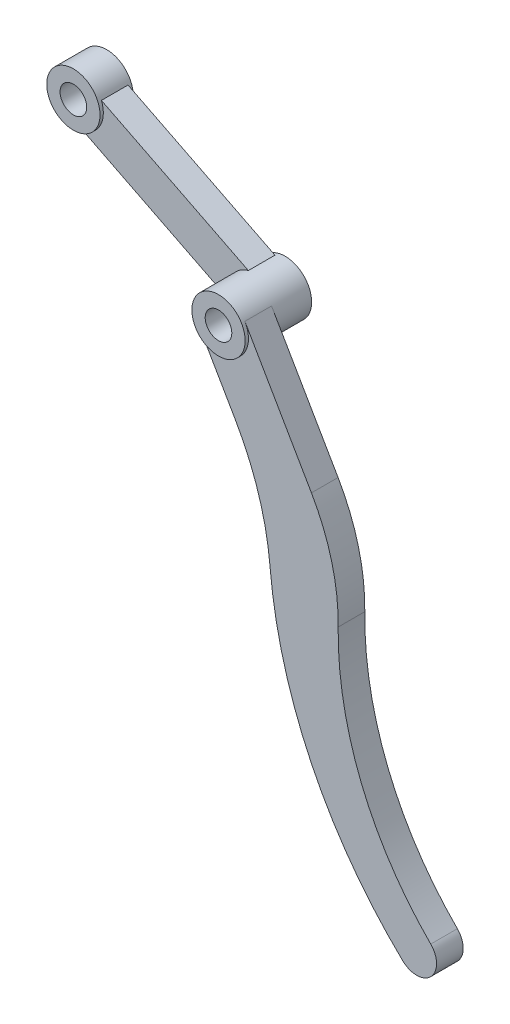
SolidWorks part; units mm, degrees
ref_plane "前视基准面" through (0, 0, 0) normal (0, 0, 1) x (1, 0, 0)
ref_plane "上视基准面" through (0, 0, 0) normal (0, 1, 0) x (1, 0, 0)
ref_plane "右视基准面" through (0, 0, 0) normal (1, 0, 0) x (0, 0, -1)
sketch "草图1" plane through (0, 0, 0) normal (0, 0, 1) x (1, 0, 0)
  circle A0 centre (0, 0) radius 4
  circle A1 centre (0, 0) radius 8
  circle A2 centre (-53.606, 26.9518) radius 4
  circle A3 centre (-53.606, 26.9518) radius 8
  dimension "D1" = 8
  dimension "D2" = 16
  dimension "D3" = 60
extrude "凸台-拉伸1" add sketch "草图1" against normal blind 10
sketch "草图3" plane through (0, 0, 0) normal (0, 0, 1) x (1, 0, 0)
  line L0 (-53.606, 26.9518) -> (0, 0) construction
  line L1 (-51.5735, 19.2143) -> (-7.4228, -2.9837)
  line L2 (-46.1832, 29.9355) -> (-2.0324, 7.7375)
  line L4 (-50.9108, 32.3124) -> (2.6952, 5.3606) construction
  line L5 (-56.3011, 21.5912) -> (-2.6952, -5.3606) construction
  circle A0 centre (0, 0) radius 8 construction
  circle A1 centre (-53.606, 26.9518) radius 8 construction
  arc A2 (-2.0324, 7.7375) -> (-7.4228, -2.9837) centre (0, 0) ccw
  arc A3 (-51.5735, 19.2143) -> (-46.1832, 29.9355) centre (-53.606, 26.9518) ccw
  dimension "D1" = 6
  dimension "D2" = 6
extrude "凸台-拉伸2" add sketch "草图3" against normal blind 8 from offset 1 contours A2 L1 A3 L2 offset against normal yes
sketch "草图4" plane through (0, 0, 0) normal (0, 0, 1) x (1, 0, 0)
  line L0 (8, 0) -> (8, -40) construction
  line L1 (-8, 0) -> (-8, -22) construction
  line L2 (81.0592, -119.5) -> (81.0592, -87.7121) construction
  line L3 (-16.4993, -145.6407) -> (81.0592, -119.5) construction
  line L4 (6.9282, 4) -> (26.9282, -30.641)
  line L5 (-6.9282, -4) -> (4.0718, -23.0526)
  line L6 (129.9493, -62.9604) -> (114.0553, -35.4313) construction
  line L7 (58.5315, -134.3782) -> (129.9493, -62.9604) construction
  circle A0 centre (0, 0) radius 8 construction
  arc A1 (-2.0324, 7.7375) -> (-7.4228, -2.9837) centre (0, 0) ccw construction
  arc A2 (-8, -22) -> (-15.4566, -55.7262) centre (-88, -22) cw construction
  arc A3 (-15.4566, -55.7262) -> (-22.2538, -147.3396) centre (102.4264, -110.5313) ccw construction
  arc A4 (-22.2538, -147.3396) -> (-10.7038, -144.0878) centre (-16.4993, -145.6407) ccw construction
  arc A5 (-10.7038, -144.0878) -> (-0.4932, -70.7742) centre (81.0592, -119.5) cw construction
  arc A6 (-0.4932, -70.7742) -> (8, -40) centre (-52, -40) ccw construction
  arc A7 (-6.9282, -4) -> (8, 0) centre (0, 0) ccw construction
  arc A8 (4.0718, -23.0526) -> (14.4773, -55.9886) centre (-65.2102, -63.0526) cw
  arc A9 (14.4773, -55.9886) -> (54.3974, -138.7267) centre (143.9695, -44.5097) ccw
  arc A10 (54.3974, -138.7267) -> (62.7742, -130.1356) centre (58.5315, -134.3782) ccw
  arc A11 (62.7742, -130.1356) -> (34.96, -61.5389) centre (129.9493, -62.9604) cw
  arc A12 (34.96, -61.5389) -> (26.9282, -30.641) centre (-25.0333, -60.641) ccw
  arc A13 (-6.9282, -4) -> (6.9282, 4) centre (0, 0) ccw construction
  arc A14 (-6.9282, -4) -> (6.9282, 4) centre (0, 0) ccw
  dimension "D3" = 95
  dimension "D4" = 130
  dimension "D5" = 6
  dimension "D6" = 80
  dimension "D7" = 60
  dimension "D8" = 119.5
  dimension "D1" = 22
  dimension "D2" = 40
  dimension "D9" = 105
  dimension "D10" = 2
extrude "凸台-拉伸3" add sketch "草图4" along normal blind 8 from offset 1
sketch "草图5" plane through (0, 0, 0) normal (0, 0, 1) x (1, 0, 0)
  circle A0 centre (0, 0) radius 8 construction
  circle A1 centre (0, 0) radius 4 construction
  circle A2 centre (0, 0) radius 8
  circle A3 centre (0, 0) radius 4
extrude "凸台-拉伸4" add sketch "草图5" along normal blind 10
